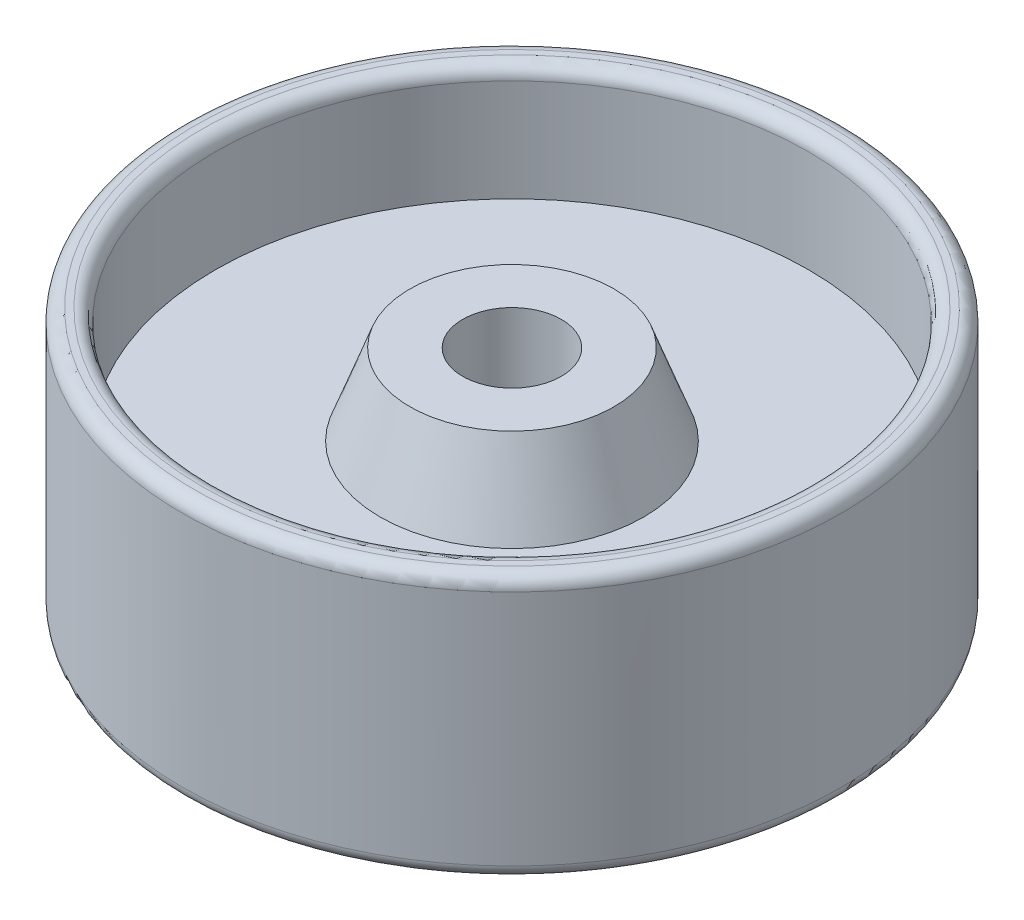
SolidWorks part; units mm, degrees
ref_plane "Front Plane" through (0, 0, 0) normal (0, 0, 1) x (1, 0, 0)
ref_plane "Top Plane" through (0, 0, 0) normal (0, 1, 0) x (1, 0, 0)
ref_plane "Right Plane" through (0, 0, 0) normal (1, 0, 0) x (0, 0, -1)
sketch "Sketch1" plane through (0, 0, 0) normal (0, 0, 1) x (1, 0, 0)
  line L0 (0, -25.4) -> (0, 25.4)
  line L1 (0, 25.4) -> (6.35, 25.4)
  line L2 (6.35, 25.4) -> (6.35, 3.175)
  line L3 (6.35, 3.175) -> (38.1, 3.175)
  line L4 (38.1, 3.175) -> (43.8275, 18.7159)
  line L5 (43.8275, 18.7159) -> (53.9875, 18.7159)
  line L6 (53.9875, 18.7159) -> (53.9875, -18.7159)
  line L7 (0, 0) -> (59.4848, 0) construction
  line L8 (63.5, 0) -> (63.5, 36.3775) construction
  line L9 (43.1496, -18.7159) -> (53.9875, -18.7159)
  line L10 (38.1, -3.175) -> (43.1496, -18.7159)
  line L11 (6.35, -3.175) -> (38.1, -3.175)
  line L12 (6.35, -25.4) -> (6.35, -3.175)
  line L13 (0, -25.4) -> (6.35, -25.4)
  point P11 (0, 0)
  point P17 (0, 0)
  point P19 (63.5, 0)
  dimension "D1" = 50.8
  dimension "D2" = 6.35
  dimension "D3" = 10.16
  dimension "D4" = 18
  dimension "D5" = 6.35
  dimension "D6" = 19.025
  dimension "D7" = 127
  dimension "D8" = 50.8
revolve "Revolve2" add sketch "Sketch1" angle 360 about L8
fillet "Fillet1" radius 2.54 3 edges at (63.5, 25.4, -57.15) (63.5, 25.4, -63.5) (63.5, -25.4, -63.5)
